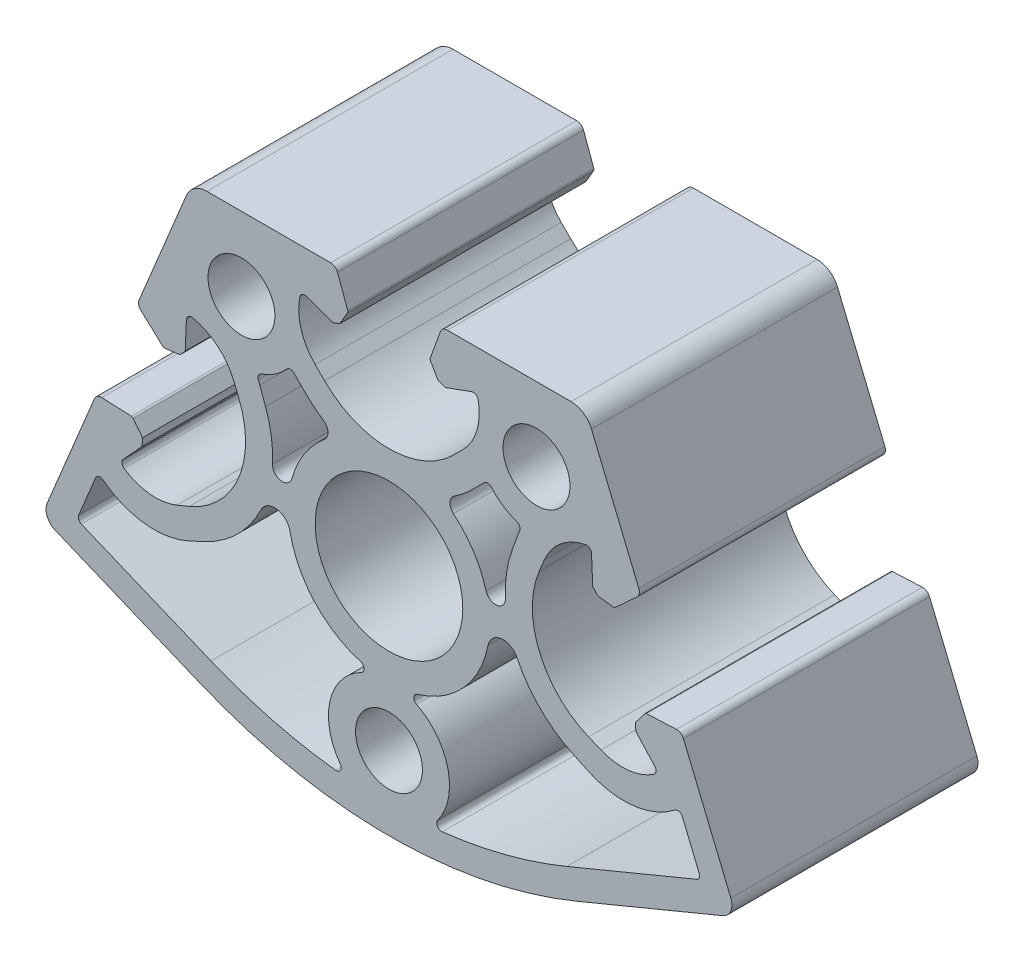
SolidWorks part; units mm, degrees
material "6005-T5"
ref_plane "Front" through (0, 0, 0) normal (0, 0, 1) x (1, 0, 0)
ref_plane "Top" through (0, 0, 0) normal (0, 1, 0) x (1, 0, 0)
ref_plane "Right" through (0, 0, 0) normal (1, 0, 0) x (0, 0, -1)
sketch "Sk Main Extrusion" plane through (0, 0, 0) normal (0, 0, 1) x (1, 0, 0)
  line L52 (9.6251, -11.5955) -> (8.4853, -12.7353)
  line L53 (12.544, -15.9595) -> (13.1248, -14.3646)
  line L54 (-13.1248, -14.3646) -> (-12.544, -15.9595)
  line L55 (-8.4853, -12.7353) -> (-9.6251, -11.5955)
  line L56 (-18.7501, -30.9423) -> (-20.2885, -31.6594)
  line L57 (-29.8125, -30.8757) -> (-31.5229, -35.005)
  line L58 (-31.2523, -35.6582) -> (-18.0818, -41.1137)
  line L59 (18.0818, -41.1137) -> (31.2523, -35.6582)
  line L60 (31.5229, -35.005) -> (29.8125, -30.8757)
  line L61 (20.2885, -31.6594) -> (18.7501, -30.9423)
  line L62 (-29.9218, -23.9533) -> (-34.7333, -35.5694)
  line L63 (-33.9215, -37.5292) -> (-19.1342, -43.6543)
  line L64 (19.1342, -43.6543) -> (33.9215, -37.5292)
  line L65 (34.7333, -35.5694) -> (29.9218, -23.9533)
  line L66 (29.1961, -23.491) -> (26.1817, -23.6226)
  line L67 (25.9943, -23.7202) -> (25.0458, -24.9563)
  line L68 (25.0458, -24.9563) -> (25.0797, -25.7334)
  line L69 (25.0797, -25.7334) -> (27.0048, -27.8343)
  line L70 (21.5385, -29.133) -> (20.2797, -28.6116)
  line L71 (15.2737, -16.5259) -> (15.7951, -15.2671)
  line L72 (20.5786, -12.3202) -> (20.7029, -15.167)
  line L73 (20.7029, -15.167) -> (21.2284, -15.7405)
  line L74 (21.2284, -15.7405) -> (22.7732, -15.9439)
  line L75 (22.9748, -15.8803) -> (25.1994, -13.8419)
  line L76 (25.3856, -13.0019) -> (20.574, -1.3858)
  line L77 (18.5, 0) -> (5.9268, 0)
  line L78 (5.2221, -0.4935) -> (4.1901, -3.3288)
  line L79 (4.2085, -3.5393) -> (4.9876, -4.8887)
  line L80 (4.9876, -4.8887) -> (5.7185, -5.1547)
  line L81 (5.7185, -5.1547) -> (8.3962, -4.1802)
  line L82 (7.5042, -9.7273) -> (6.5407, -10.6907)
  line L83 (-6.5407, -10.6907) -> (-7.5042, -9.7273)
  line L84 (-8.3962, -4.1802) -> (-5.7185, -5.1547)
  line L85 (-5.7185, -5.1547) -> (-4.9876, -4.8887)
  line L86 (-4.9876, -4.8887) -> (-4.2085, -3.5393)
  line L87 (-4.1901, -3.3288) -> (-5.2221, -0.4935)
  line L88 (-5.9268, 0) -> (-18.5, 0)
  line L89 (-20.574, -1.3858) -> (-25.3856, -13.0019)
  line L90 (-25.1994, -13.8419) -> (-22.9748, -15.8803)
  line L91 (-22.7732, -15.9439) -> (-21.2284, -15.7405)
  line L92 (-21.2284, -15.7405) -> (-20.7029, -15.167)
  line L93 (-20.7029, -15.167) -> (-20.5786, -12.3202)
  line L94 (-15.7951, -15.2671) -> (-15.2737, -16.5259)
  line L95 (-20.2797, -28.6116) -> (-21.5385, -29.133)
  line L96 (-27.0048, -27.8343) -> (-25.0797, -25.7334)
  line L97 (-25.0797, -25.7334) -> (-25.0458, -24.9563)
  line L98 (-25.0458, -24.9563) -> (-25.9943, -23.7202)
  line L99 (-26.1817, -23.6226) -> (-29.1961, -23.491)
  circle A76 centre (0, -39.9603) radius 3.4
  circle A77 centre (0, -23.7302) radius 7.5
  circle A78 centre (-14.9887, -7.5) radius 3.4
  circle A79 centre (14.9887, -7.5) radius 3.4
  arc A80 (10.3882, -11.5815) -> (9.6586, -11.5617) centre (10.0142, -11.9133) ccw
  arc A81 (9.6251, -11.5955) -> (9.6586, -11.5617) centre (3.65, -5.6205) ccw
  arc A82 (6.6388, -14.2463) -> (8.4853, -12.7353) centre (0, -4.25) ccw
  arc A83 (6.6388, -14.2463) -> (6.5528, -15.8483) centre (7.192, -15.0793) ccw
  arc A84 (9.8721, -20.9726) -> (6.5528, -15.8483) centre (0, -23.7302) ccw
  arc A85 (9.8721, -20.9726) -> (11.834, -20.6545) centre (10.8352, -20.7036) ccw
  arc A86 (12.544, -15.9595) -> (11.834, -20.6545) centre (23.8196, -20.0657) ccw
  arc A87 (13.2761, -13.9787) -> (13.1248, -14.3646) centre (21.0647, -17.2561) ccw
  arc A88 (13.2761, -13.9787) -> (12.9787, -13.3123) centre (12.8153, -13.7848) ccw
  arc A89 (10.3882, -11.5815) -> (12.9787, -13.3123) centre (14.9887, -7.5) ccw
  arc A90 (-29.1961, -23.491) -> (-29.9218, -23.9533) centre (-29.2289, -24.2403) ccw
  arc A91 (-34.7333, -35.5694) -> (-33.9215, -37.5292) centre (-33.3475, -36.1434) ccw
  arc A92 (-19.1342, -43.6543) -> (19.1342, -43.6543) centre (0, 2.5397) ccw
  arc A93 (33.9215, -37.5292) -> (34.7333, -35.5694) centre (33.3475, -36.1434) ccw
  arc A94 (29.9218, -23.9533) -> (29.1961, -23.491) centre (29.2289, -24.2403) ccw
  arc A95 (26.1817, -23.6226) -> (25.9943, -23.7202) centre (26.1926, -23.8724) ccw
  arc A96 (26.9166, -28.5861) -> (27.0048, -27.8343) centre (26.6362, -28.1721) ccw
  arc A97 (21.5385, -29.133) -> (26.9166, -28.5861) centre (23.7198, -23.8669) ccw
  arc A98 (15.2737, -16.5259) -> (20.2797, -28.6116) centre (23.8196, -20.0657) ccw
  arc A99 (19.9847, -11.851) -> (15.7951, -15.2671) centre (21.0612, -17.4484) ccw
  arc A100 (20.5786, -12.3202) -> (19.9847, -11.851) centre (20.0791, -12.342) ccw
  arc A101 (22.7732, -15.9439) -> (22.9748, -15.8803) centre (22.8059, -15.696) ccw
  arc A102 (25.1994, -13.8419) -> (25.3856, -13.0019) centre (24.6927, -13.2889) ccw
  arc A103 (20.574, -1.3858) -> (18.5, 0) centre (18.5, -2.2449) ccw
  arc A104 (5.9268, 0) -> (5.2221, -0.4935) centre (5.9268, -0.75) ccw
  arc A105 (4.1901, -3.3288) -> (4.2085, -3.5393) centre (4.425, -3.4143) ccw
  arc A106 (9.057, -4.5493) -> (8.3962, -4.1802) centre (8.5672, -4.65) ccw
  arc A107 (7.5042, -9.7273) -> (9.057, -4.5493) centre (3.4737, -5.6968) ccw
  arc A108 (-6.5407, -10.6907) -> (6.5407, -10.6907) centre (0, -4.15) ccw
  arc A109 (-9.057, -4.5493) -> (-7.5042, -9.7273) centre (-3.4737, -5.6968) ccw
  arc A110 (-8.3962, -4.1802) -> (-9.057, -4.5493) centre (-8.5672, -4.65) ccw
  arc A111 (-4.2085, -3.5393) -> (-4.1901, -3.3288) centre (-4.425, -3.4143) ccw
  arc A112 (-5.2221, -0.4935) -> (-5.9268, 0) centre (-5.9268, -0.75) ccw
  arc A113 (-18.5, 0) -> (-20.574, -1.3858) centre (-18.5, -2.2449) ccw
  arc A114 (-25.3856, -13.0019) -> (-25.1994, -13.8419) centre (-24.6927, -13.2889) ccw
  arc A115 (-22.9748, -15.8803) -> (-22.7732, -15.9439) centre (-22.8059, -15.696) ccw
  arc A116 (-19.9847, -11.851) -> (-20.5786, -12.3202) centre (-20.0791, -12.342) ccw
  arc A117 (-15.7951, -15.2671) -> (-19.9847, -11.851) centre (-21.0612, -17.4484) ccw
  arc A118 (-20.2797, -28.6116) -> (-15.2737, -16.5259) centre (-23.8196, -20.0657) ccw
  arc A119 (-26.9166, -28.5861) -> (-21.5385, -29.133) centre (-23.7198, -23.8669) ccw
  arc A120 (-27.0048, -27.8343) -> (-26.9166, -28.5861) centre (-26.6362, -28.1721) ccw
  arc A121 (-25.9943, -23.7202) -> (-26.1817, -23.6226) centre (-26.1926, -23.8724) ccw
  arc A122 (-9.6586, -11.5617) -> (-9.6251, -11.5955) centre (-3.65, -5.6205) ccw
  arc A123 (-9.6586, -11.5617) -> (-10.3882, -11.5815) centre (-10.0142, -11.9133) ccw
  arc A124 (-12.9787, -13.3123) -> (-10.3882, -11.5815) centre (-14.9887, -7.5) ccw
  arc A125 (-12.9787, -13.3123) -> (-13.2761, -13.9787) centre (-12.8153, -13.7848) ccw
  arc A126 (-13.1248, -14.3646) -> (-13.2761, -13.9787) centre (-21.0647, -17.2561) ccw
  arc A127 (-11.834, -20.6545) -> (-12.544, -15.9595) centre (-23.8196, -20.0657) ccw
  arc A128 (-11.834, -20.6545) -> (-9.8721, -20.9726) centre (-10.8352, -20.7036) ccw
  arc A129 (-6.5528, -15.8483) -> (-9.8721, -20.9726) centre (0, -23.7302) ccw
  arc A130 (-6.5528, -15.8483) -> (-6.6388, -14.2463) centre (-7.192, -15.0793) ccw
  arc A131 (-8.4853, -12.7353) -> (-6.6388, -14.2463) centre (0, -4.25) ccw
  arc A132 (-10.0652, -25.6677) -> (-13.0131, -25.2829) centre (-11.6029, -25.9638) ccw
  arc A133 (-18.7501, -30.9423) -> (-13.0131, -25.2829) centre (-23.8196, -20.0657) ccw
  arc A134 (-29.0438, -30.6722) -> (-20.2885, -31.6594) centre (-23.8583, -24.0004) ccw
  arc A135 (-29.0438, -30.6722) -> (-29.8125, -30.8757) centre (-29.3506, -31.067) ccw
  arc A136 (-31.5229, -35.005) -> (-31.2523, -35.6582) centre (-31.061, -35.1963) ccw
  arc A137 (-18.0818, -41.1137) -> (-5.4128, -44.3993) centre (0, 2.5397) ccw
  arc A138 (-5.4128, -44.3993) -> (-4.9528, -43.6062) centre (-5.3555, -43.9026) ccw
  arc A139 (-2.8063, -34.4879) -> (-4.9528, -43.6062) centre (0, -39.9603) ccw
  arc A140 (-2.8063, -34.4879) -> (-2.8933, -33.5634) centre (-3.0344, -34.043) ccw
  arc A141 (-10.0652, -25.6677) -> (-2.8933, -33.5634) centre (0, -23.7302) ccw
  arc A142 (13.0131, -25.2829) -> (10.0652, -25.6677) centre (11.6029, -25.9638) ccw
  arc A143 (2.8933, -33.5634) -> (10.0652, -25.6677) centre (0, -23.7302) ccw
  arc A144 (2.8933, -33.5634) -> (2.8063, -34.4879) centre (3.0344, -34.043) ccw
  arc A145 (4.9528, -43.6062) -> (2.8063, -34.4879) centre (0, -39.9603) ccw
  arc A146 (4.9528, -43.6062) -> (5.4128, -44.3993) centre (5.3555, -43.9026) ccw
  arc A147 (5.4128, -44.3993) -> (18.0818, -41.1137) centre (0, 2.5397) ccw
  arc A148 (31.2523, -35.6582) -> (31.5229, -35.005) centre (31.061, -35.1963) ccw
  arc A149 (29.8125, -30.8757) -> (29.0438, -30.6722) centre (29.3506, -31.067) ccw
  arc A150 (20.2885, -31.6594) -> (29.0438, -30.6722) centre (23.8583, -24.0004) ccw
  arc A151 (13.0131, -25.2829) -> (18.7501, -30.9423) centre (23.8196, -20.0657) ccw
  point P171 (0, 0)
extrude "Main Extrusion" add sketch "Sk Main Extrusion" against normal blind 25
sketch "Threaded Insert Mate Sketch" plane through (0, 0, 0) normal (0, 0, 1) x (1, 0, 0)
  line L1 (25.3856, -13.0019) -> (29.9218, -23.9533) construction
  line L2 (27.6537, -18.4776) -> (20.9093, -21.2712) construction
  line L4 (0, -7.3) -> (0, -31.2302) construction
  line L5 (18.5, 0) -> (5.9268, 0) construction
  circle A0 centre (0, -7.3) radius 5.6515
  circle A1 centre (20.9093, -21.2712) radius 5.6515
  circle A3 centre (-20.9093, -21.2712) radius 5.6515
  circle A4 centre (0, -23.7302) radius 7.5 construction
equation "\"Weight kg\"= round ( \"SW-Mass\" , 2 )"
equation "\"Weight lbs\"= round ( \"SW-Mass\" * 2.2046 , 2 )"
equation "\"Length mm\"= round ( \"Length@Main Extrusion\" , 2 )"
equation "\"Length in\"= round ( \"Length@Main Extrusion\" / 25.4 , 3 )"
equation "\"D3@Threaded Insert Mate Sketch\"=\"D2@Threaded Insert Mate Sketch\""
